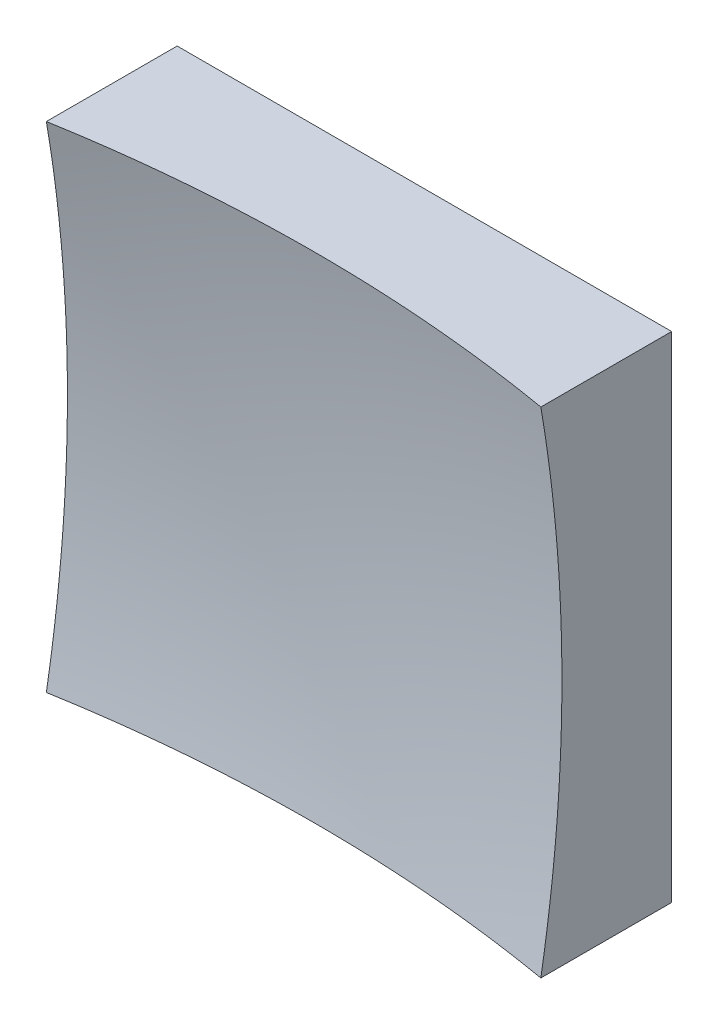
SolidWorks part; units mm, degrees
ref_plane "前视基准面" through (0, 0, 0) normal (0, 0, 1) x (1, 0, 0)
ref_plane "上视基准面" through (0, 0, 0) normal (0, 1, 0) x (1, 0, 0)
ref_plane "右视基准面" through (0, 0, 0) normal (1, 0, 0) x (0, 0, -1)
sketch "草图1" plane through (0, 0, 0) normal (0, 0, 1) x (1, 0, 0)
  line L1 (-25, 25) -> (25, 25)
  line L2 (-25, 25) -> (-25, -25)
  line L3 (-25, -25) -> (25, -25)
  line L4 (25, 25) -> (25, -25)
  line L5 (-25, 25) -> (25, -25) construction
  line L6 (-25, -25) -> (25, 25) construction
  point P0 (0, 0)
  dimension "D1" = 50
  dimension "D2" = 50
extrude "凸台-拉伸1" add sketch "草图1" along normal blind 50 contours L2 L3 L4 L1
sketch "草图2" plane through (0, 0, 0) normal (0, 1, 0) x (1, 0, 0)
  line L0 (-7.4603, -9) -> (7.3192, -9) construction
  line L1 (0, 0) -> (0, -12.1749) construction
  line L2 (146.2268, -125.5677) -> (0, -125.5677)
  line L3 (0, -125.5677) -> (0, -9)
  arc A1 (146.2268, -125.5677) -> (0, -9) centre (0, -159) ccw
  dimension "D2" = 300
  dimension "D1" = 9
revolve "切除-旋转2" cut sketch "草图2" angle 360 about L3
